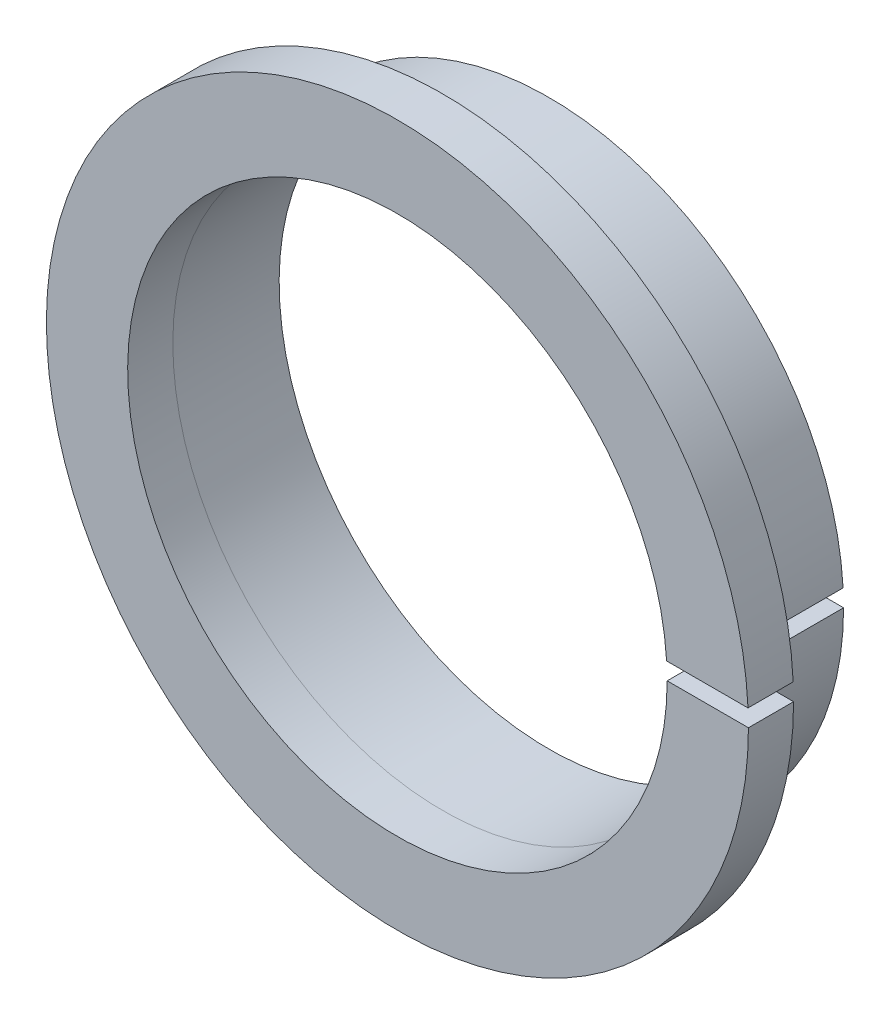
SolidWorks part; units mm, degrees
ref_plane "Front Plane" through (0, 0, 0) normal (0, 0, 1) x (1, 0, 0)
ref_plane "Top Plane" through (0, 0, 0) normal (0, 1, 0) x (1, 0, 0)
ref_plane "Right Plane" through (0, 0, 0) normal (1, 0, 0) x (0, 0, -1)
sketch "Sketch1" plane through (0, 0, 0) normal (0, 0, 1) x (1, 0, 0)
  line L4 (11.9259, 0.75) -> (15.5312, 0.7501)
  line L5 (15.5493, 0) -> (11.9495, 0)
  arc A3 (11.9259, 0.75) -> (11.9495, 0) centre (0, 0) ccw
  arc A4 (15.5312, 0.7501) -> (15.5493, 0) centre (0, 0) ccw
  dimension "D1" = 11.9494
  dimension "D2" = 15.5493
  dimension "D3" = 3.6053
  dimension "D4" = 0.75
extrude "Boss-Extrude2" add sketch "Sketch1" against normal blind 2 separate body
sketch "Sketch2" plane through (0, 0, -2) normal (0, 0, -1) x (-1, 0, 0)
  line L4 (-11.9494, 0) -> (-13.0544, 0)
  line L5 (-13.0328, 0.75) -> (-11.9259, 0.75)
  arc A0 (-15.5493, 0) -> (-15.5312, 0.7501) centre (0, 0) ccw construction
  arc A3 (-11.9494, 0) -> (-11.9259, 0.75) centre (0, 0) ccw
  arc A4 (-13.0544, 0) -> (-13.0328, 0.75) centre (0, 0) ccw
  dimension "D1" = 13.0544
  dimension "D2" = 11.9494
  dimension "D3" = 1.105
  dimension "D4" = 1.1069
  dimension "D5" = 0.75
extrude "Boss-Extrude3" add sketch "Sketch2" along normal blind 4.71 separate body
